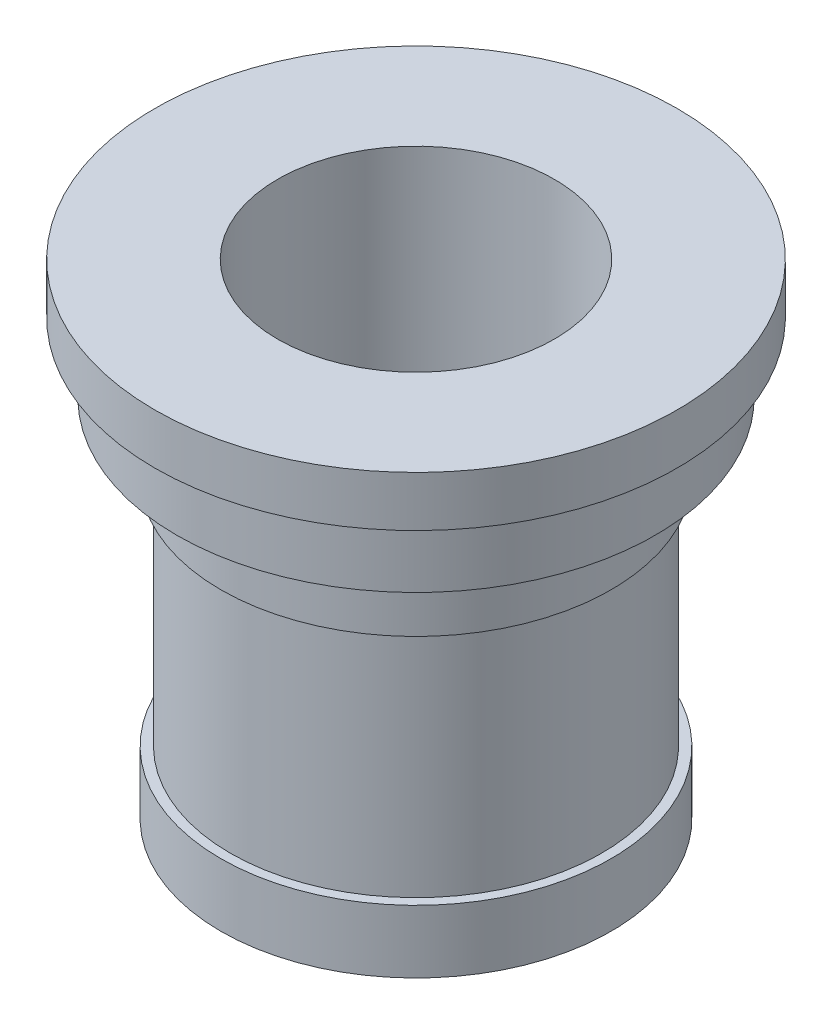
SolidWorks part; units mm, degrees
ref_plane "Front Plane" through (0, 0, 0) normal (0, 0, 1) x (1, 0, 0)
ref_plane "Top Plane" through (0, 0, 0) normal (0, 1, 0) x (1, 0, 0)
ref_plane "Right Plane" through (0, 0, 0) normal (1, 0, 0) x (0, 0, -1)
sketch "Sketch3" plane through (0, 0, 0) normal (0, 0, 1) x (1, 0, 0)
  line L0 (0, 98.3175) -> (0, -75.2372) construction
  line L1 (0, 0) -> (31, 0)
  line L2 (31, 0) -> (31, 10)
  line L3 (31, 10) -> (29.5, 10)
  line L4 (29.5, 10) -> (29.5, 47)
  line L5 (29.5, 47) -> (31, 47)
  line L6 (31, 47) -> (31, 58)
  line L7 (31, 58) -> (38, 58)
  line L8 (38, 58) -> (38, 69)
  line L9 (38, 69) -> (41.5, 69)
  line L10 (41.5, 69) -> (41.5, 77)
  line L11 (41.5, 77) -> (0, 77)
  line L12 (0, 77) -> (0, 0)
  dimension "D1" = 62
  dimension "D2" = 59
  dimension "D3" = 62
  dimension "D4" = 76
  dimension "D5" = 83
  dimension "D6" = 10
  dimension "D7" = 77
  dimension "D8" = 8
  dimension "D9" = 11
  dimension "D10" = 11
revolve "Revolve1" add sketch "Sketch3" angle 360 about L0
sketch "Sketch4" plane through (0, 77, 0) normal (0, 1, 0) x (1, 0, 0)
  circle A0 centre (0, 0) radius 22
  dimension "D1" = 44
extrude "Cut-Extrude1" cut sketch "Sketch4" against normal through all
sketch "Sketch5" plane through (0, 0, 0) normal (0, -1, 0) x (-1, 0, 0)
  circle A0 centre (0, 22) radius 1.5
  dimension "D1" = 3
  dimension "D2" = 22
extrude "Cut-Extrude2" cut sketch "Sketch5" against normal blind 10
